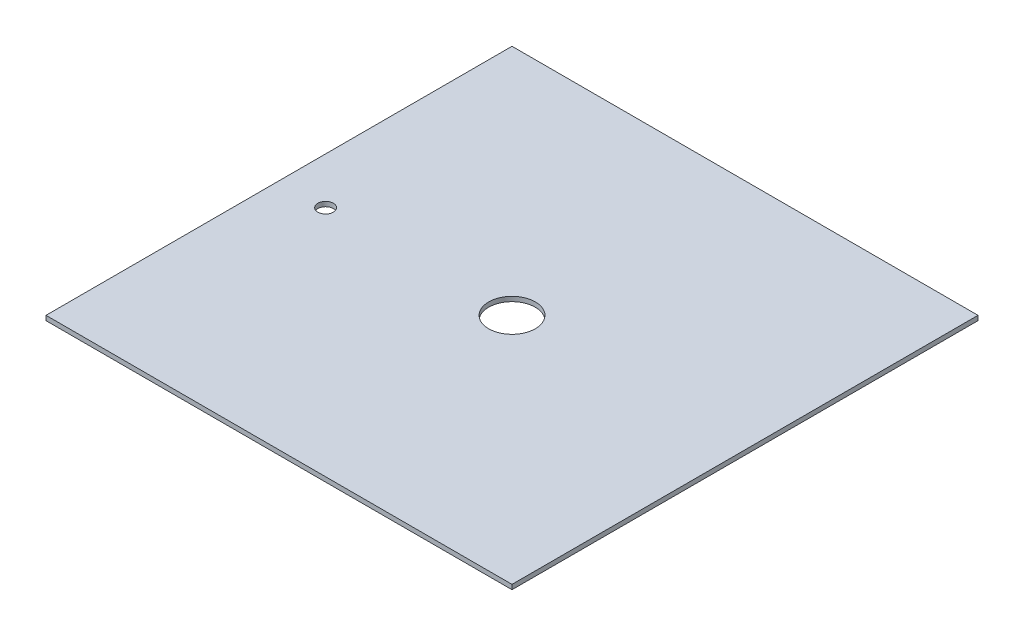
SolidWorks part; units mm, degrees
ref_plane "Front Plane" through (0, 0, 0) normal (0, 0, 1) x (1, 0, 0)
ref_plane "Top Plane" through (0, 0, 0) normal (0, 1, 0) x (1, 0, 0)
ref_plane "Right Plane" through (0, 0, 0) normal (1, 0, 0) x (0, 0, -1)
sketch "Sketch2" plane through (0, 0, 0) normal (0, 1, 0) x (1, 0, 0)
  line L1 (-150, 150) -> (150, 150)
  line L2 (-150, 150) -> (-150, -150)
  line L3 (-150, -150) -> (150, -150)
  line L4 (150, 150) -> (150, -150)
  line L5 (-150, 150) -> (150, -150) construction
  line L6 (-150, -150) -> (150, 150) construction
  point P0 (0, 0)
  dimension "D1" = 300
  dimension "D2" = 300
extrude "Boss-Extrude1" add sketch "Sketch2" along normal blind 3
sketch "Sketch3" plane through (0, 3, 0) normal (0, 1, 0) x (1, 0, 0)
  circle A0 centre (0, 0) radius 15
  dimension "D1" = 30
extrude "Cut-Extrude1" cut sketch "Sketch3" against normal through all
sketch "Sketch4" plane through (0, 3, 0) normal (0, 1, 0) x (1, 0, 0)
  line L0 (-150, 150) -> (-150, -150) construction
  circle A0 centre (-120, 0) radius 5
  dimension "D1" = 10
  dimension "D2" = 30
extrude "Cut-Extrude2" cut sketch "Sketch4" against normal through all
